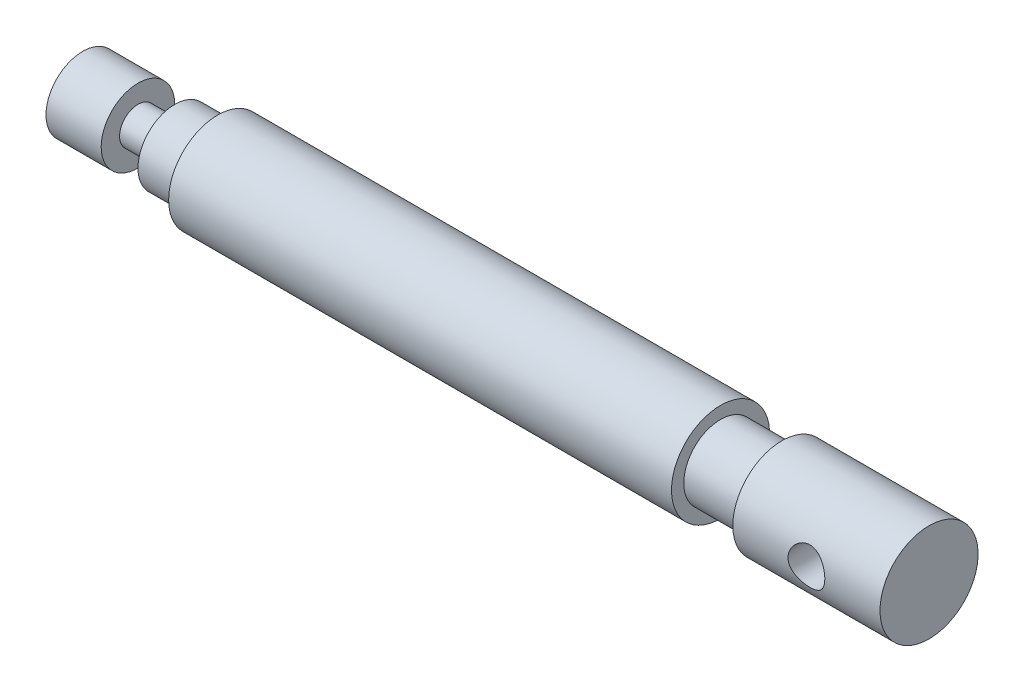
SolidWorks part; units mm, degrees
ref_plane "Front Plane" through (0, 0, 0) normal (0, 0, 1) x (1, 0, 0)
ref_plane "Top Plane" through (0, 0, 0) normal (0, 1, 0) x (1, 0, 0)
ref_plane "Right Plane" through (0, 0, 0) normal (1, 0, 0) x (0, 0, -1)
sketch "Sketch1" plane through (0, 0, 0) normal (0, 0, 1) x (1, 0, 0)
  line L0 (0, 0) -> (11932.2918, 0) construction
  line L1 (0, 0) -> (0, 6)
  line L2 (0, 6) -> (9, 6)
  line L3 (9, 6) -> (9, 3)
  line L4 (9, 3) -> (15, 3)
  line L5 (15, 3) -> (15, 6)
  line L6 (15, 6) -> (22, 6)
  line L7 (22, 6) -> (22, 8)
  line L8 (22, 8) -> (104, 8)
  line L9 (104, 8) -> (104, 6)
  line L10 (104, 6) -> (114, 6)
  line L11 (114, 6) -> (114, 8)
  line L12 (114, 8) -> (138, 8)
  line L13 (138, 8) -> (138, 0)
  line L14 (138, 0) -> (0, 0)
  dimension "D1" = 138
  dimension "D2" = 24
  dimension "D3" = 9
  dimension "D4" = 10
  dimension "D5" = 6
  dimension "D6" = 82
  dimension "D7" = 12
  dimension "D8" = 6
  dimension "D9" = 16
  dimension "D10" = 12
revolve "Revolve1" add sketch "Sketch1" angle 360 about L0
sketch "Sketch2" plane through (0, 0, 0) normal (0, 0, 1) x (1, 0, 0)
  line L0 (138, -8) -> (138, 8) construction
  circle A0 centre (126, 0) radius 3
  dimension "D1" = 6
  dimension "D2" = 12
extrude "Cut-Extrude1" cut sketch "Sketch2" against normal through all both and the other way through all
